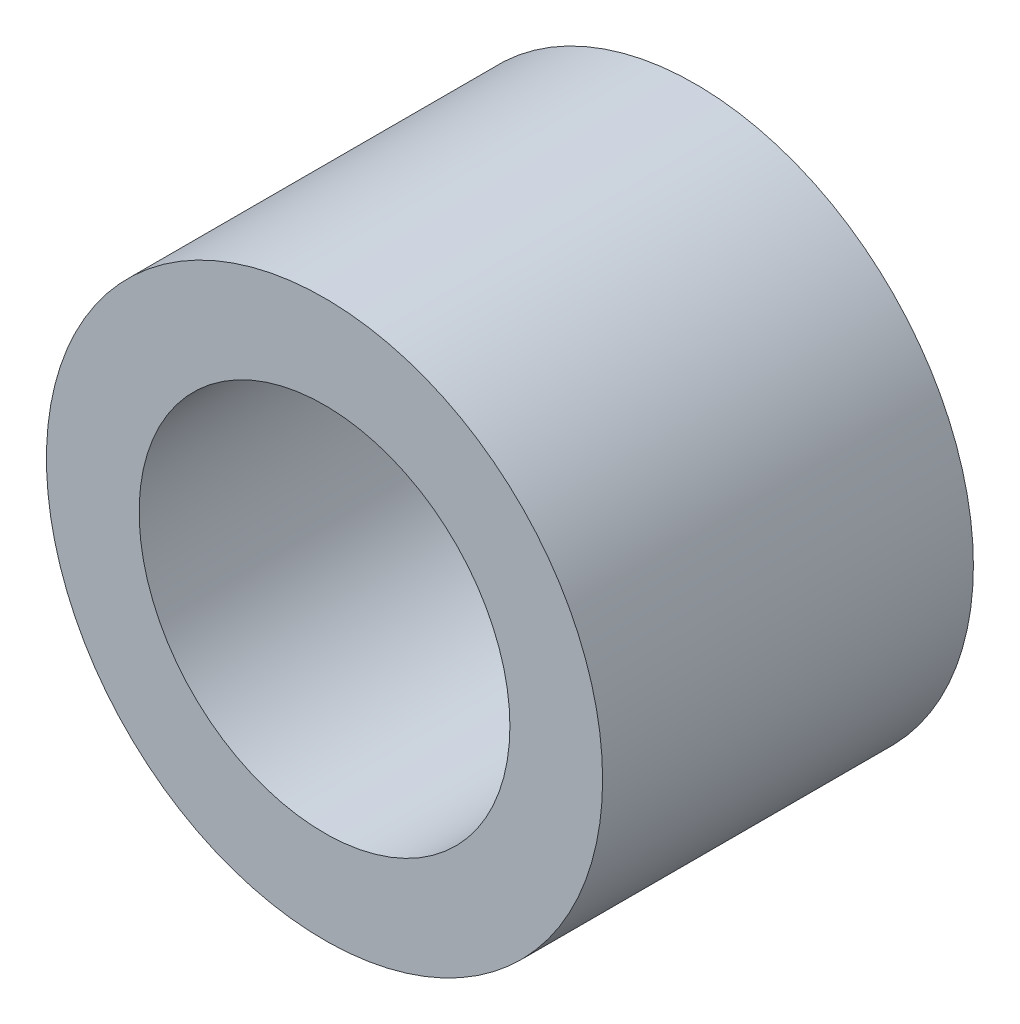
SolidWorks part; units mm, degrees
ref_plane "Front Plane" through (0, 0, 0) normal (0, 0, 1) x (1, 0, 0)
ref_plane "Top Plane" through (0, 0, 0) normal (0, 1, 0) x (1, 0, 0)
ref_plane "Right Plane" through (0, 0, 0) normal (1, 0, 0) x (0, 0, -1)
sketch "Sketch1" plane through (0, 0, 0) normal (0, 0, 1) x (1, 0, 0)
  circle A0 centre (0, 0) radius 2
  circle A1 centre (0, 0) radius 3
  dimension "D1" = 4
  dimension "D2" = 1
extrude "Boss-Extrude1" add sketch "Sketch1" along normal blind 4
